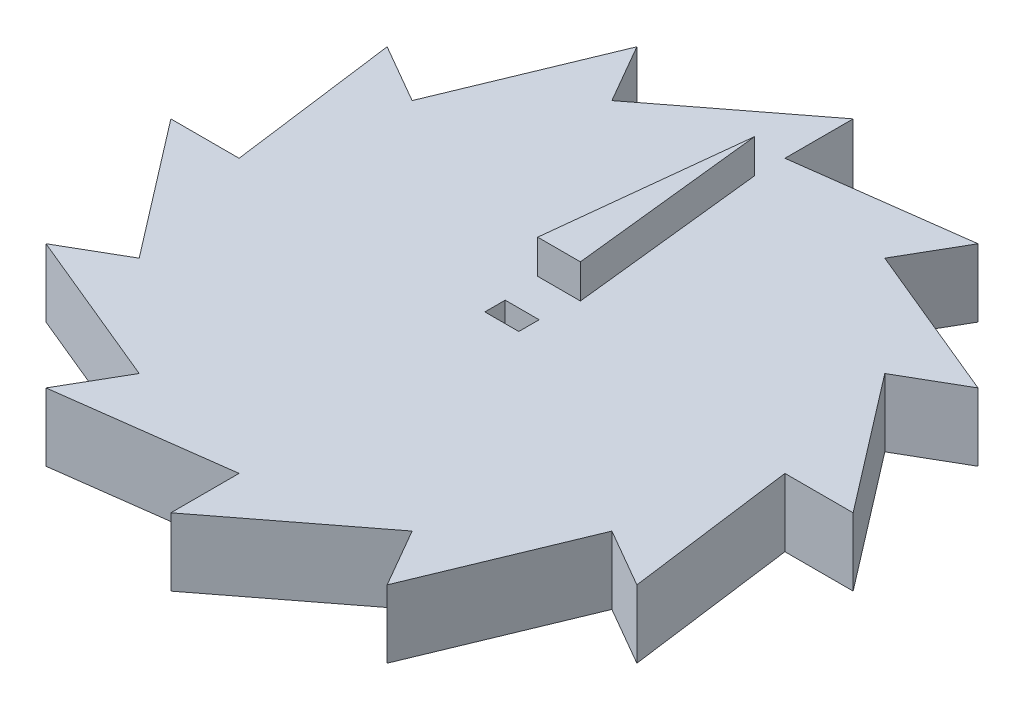
SolidWorks part; units mm, degrees
ref_plane "Front Plane" through (0, 0, 0) normal (0, 0, 1) x (1, 0, 0)
ref_plane "Top Plane" through (0, 0, 0) normal (0, 1, 0) x (1, 0, 0)
ref_plane "Right Plane" through (0, 0, 0) normal (1, 0, 0) x (0, 0, -1)
sketch "Sketch2" plane through (0, 0, 0) normal (0, 1, 0) x (1, 0, 0)
  line L0 (0, 40.2234) -> (0, 50.2793)
  line L1 (20.1117, 34.8345) -> (25.1396, 43.5431)
  line L2 (34.8345, 20.1117) -> (43.5431, 25.1396)
  line L3 (40.2234, 0) -> (50.2793, 0)
  line L4 (34.8345, -20.1117) -> (43.5431, -25.1396)
  line L5 (20.1117, -34.8345) -> (25.1396, -43.5431)
  line L6 (0, -40.2234) -> (0, -50.2793)
  line L7 (-20.1117, -34.8345) -> (-25.1396, -43.5431)
  line L8 (-34.8345, -20.1117) -> (-43.5431, -25.1396)
  line L9 (-40.2234, 0) -> (-50.2793, 0)
  line L10 (-34.8345, 20.1117) -> (-43.5431, 25.1396)
  line L11 (-20.1117, 34.8345) -> (-25.1396, 43.5431)
  line L12 (0, 50.2793) -> (-20.1117, 34.8345)
  line L13 (25.1396, 43.5431) -> (0, 40.2234)
  line L14 (43.5431, 25.1396) -> (20.1117, 34.8345)
  line L15 (50.2793, 0) -> (34.8345, 20.1117)
  line L16 (43.5431, -25.1396) -> (40.2234, 0)
  line L17 (25.1396, -43.5431) -> (34.8345, -20.1117)
  line L18 (0, -50.2793) -> (20.1117, -34.8345)
  line L19 (-25.1396, -43.5431) -> (0, -40.2234)
  line L20 (-43.5431, -25.1396) -> (-20.1117, -34.8345)
  line L21 (-50.2793, 0) -> (-34.8345, -20.1117)
  line L22 (-43.5431, 25.1396) -> (-40.2234, 0)
  line L23 (-25.1396, 43.5431) -> (-34.8345, 20.1117)
  line L25 (-2.5, 1.5) -> (2.5, 1.5)
  line L26 (-2.5, 1.5) -> (-2.5, -1.5)
  line L27 (-2.5, -1.5) -> (2.5, -1.5)
  line L28 (2.5, 1.5) -> (2.5, -1.5)
  circle A1 centre (0, 0) radius 40.2234 construction
  point P18 (0, 0)
  dimension "D1" = 12
  dimension "D2" = 5
  dimension "D3" = 2.5
  dimension "D4" = 3
  dimension "D5" = 1.5
extrude "Boss-Extrude2" add sketch "Sketch2" along normal blind 10
sketch "Sketch3" plane through (0, 10, 0) normal (0, 1, 0) x (1, 0, 0)
  line L0 (0, 35.7619) -> (-3.15, 6.9334)
  line L1 (0, 35.7619) -> (3.15, 6.9334)
  line L2 (3.15, 6.9334) -> (-3.15, 6.9334)
  dimension "D1" = 6.3
  dimension "D2" = 29
  dimension "D3" = 29
  dimension "D4" = 0
extrude "Boss-Extrude3" add sketch "Sketch3" along normal blind 5
